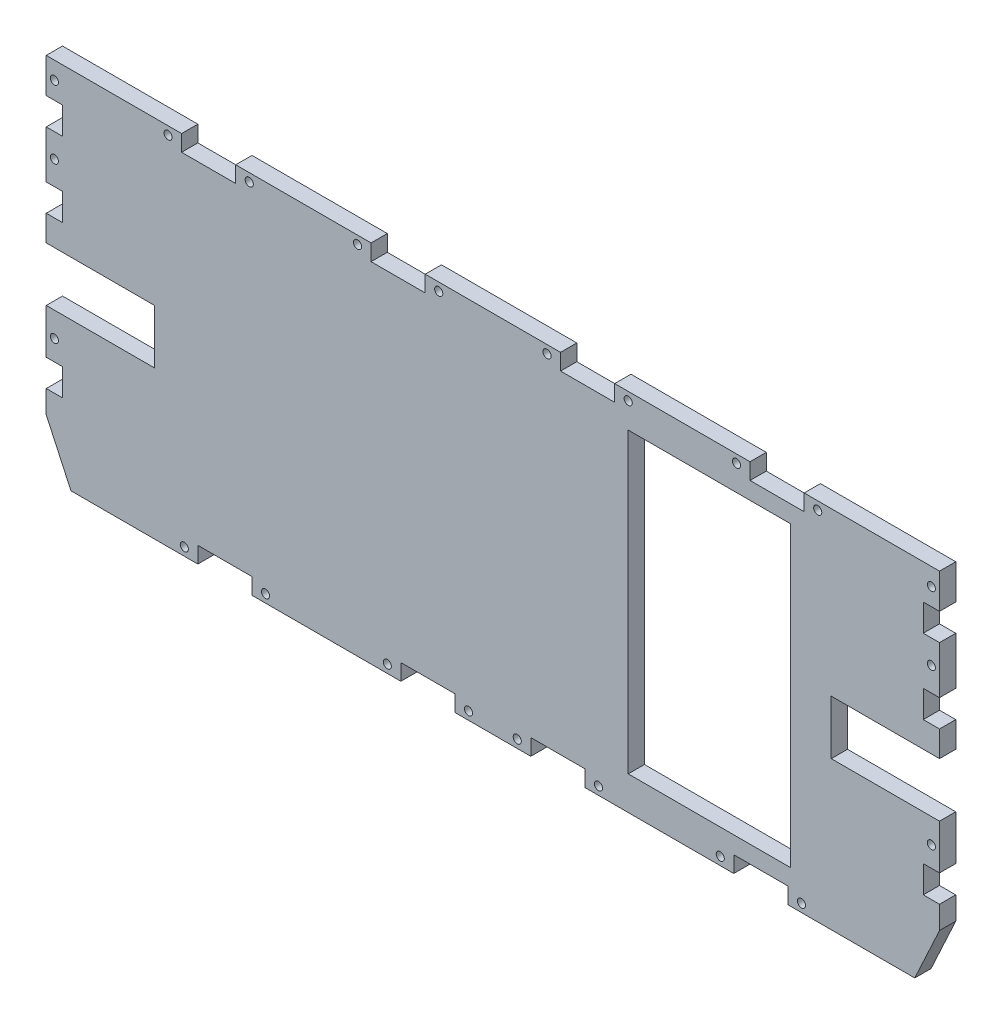
SolidWorks part; units mm, degrees
ref_plane "Plan de face" through (0, 0, 0) normal (0, 0, 1) x (1, 0, 0)
ref_plane "Plan de dessus" through (0, 0, 0) normal (0, 1, 0) x (1, 0, 0)
ref_plane "Plan de droite" through (0, 0, 0) normal (1, 0, 0) x (0, 0, -1)
sketch "Esquisse1" plane through (0, 0, 0) normal (0, 0, 1) x (1, 0, 0)
  line L0 (0, 124.9429) -> (0, -204.46) construction
  line L1 (-165, 96.73) -> (165, 96.73)
  line L2 (165, 96.73) -> (165, -18.27)
  line L3 (165, -18.27) -> (123, -109.0224)
  line L4 (123, -109.0224) -> (-123, -109.0224)
  line L5 (-211.9802, 0) -> (248.5953, 0) construction
  line L6 (-123, -109.0224) -> (-165, -18.27)
  line L7 (-165, -18.27) -> (-165, 96.73)
  dimension "D2" = 165
  dimension "D3" = 330
  dimension "D4" = 100
  dimension "D5" = 115
  dimension "D6" = 100
  dimension "D7" = 246
  dimension "D8" = 205.7524
  dimension "D9" = 96.73
  dimension "D10" = 115
extrude "Boss.-Extru.1" add sketch "Esquisse1" along normal blind 6
sketch "Esquisse3" plane through (0, 0, 0) normal (0, 0, -1) x (-1, 0, 0)
  line L0 (165, 96.73) -> (165, -18.27) construction
  line L1 (165, -9.85) -> (159, -9.85)
  line L2 (165, -9.85) -> (165, 0.15)
  line L3 (165, 0.15) -> (159, 0.15)
  line L4 (159, -9.85) -> (159, 0.15)
  line L5 (123, -109.0224) -> (-123, -109.0224) construction
  line L6 (165, 73.8526) -> (159, 73.8526)
  line L7 (165, 73.8526) -> (165, 83.8526)
  line L8 (165, 83.8526) -> (159, 83.8526)
  line L9 (159, 73.8526) -> (159, 83.8526)
  line L10 (-14, -38.02) -> (-14, -32.02)
  line L11 (109, -38.02) -> (89, -38.02)
  line L12 (109, -38.02) -> (109, -32.02)
  line L13 (109, -32.02) -> (89, -32.02)
  line L14 (-159, 46.23) -> (-159, 56.23)
  line L15 (0, -209.4812) -> (0, 177.1799) construction
  line L16 (-110, 84.355) -> (-50, 84.355)
  line L17 (-165, 56.23) -> (-159, 56.23)
  line L18 (89, -38.02) -> (89, -32.02)
  line L19 (34, -38.02) -> (14, -38.02)
  line L20 (34, -38.02) -> (34, -32.02)
  line L21 (34, -32.02) -> (14, -32.02)
  line L22 (-159, 73.8526) -> (-159, 83.8526)
  line L23 (-165, 83.8526) -> (-159, 83.8526)
  line L24 (-165, 73.8526) -> (-165, 83.8526)
  line L25 (-165, 73.8526) -> (-159, 73.8526)
  line L26 (-159, -9.85) -> (-159, 0.15)
  line L27 (-165, 0.15) -> (-159, 0.15)
  line L28 (-165, -9.85) -> (-165, 0.15)
  line L29 (-165, -9.85) -> (-159, -9.85)
  line L30 (-165, 96.73) -> (165, 96.73) construction
  line L31 (115, 96.73) -> (95, 96.73)
  line L32 (115, 96.73) -> (115, 90.73)
  line L33 (115, 90.73) -> (95, 90.73)
  line L34 (95, 96.73) -> (95, 90.73)
  line L35 (-25, 96.73) -> (-25, 90.73)
  line L36 (45, 96.73) -> (25, 96.73)
  line L37 (45, 96.73) -> (45, 90.73)
  line L38 (45, 90.73) -> (25, 90.73)
  line L39 (25, 96.73) -> (25, 90.73)
  line L40 (-45, 90.73) -> (-25, 90.73)
  line L41 (-45, 96.73) -> (-45, 90.73)
  line L42 (-45, 96.73) -> (-25, 96.73)
  line L43 (-95, 96.73) -> (-95, 90.73)
  line L44 (-115, 90.73) -> (-95, 90.73)
  line L45 (-115, 96.73) -> (-115, 90.73)
  line L46 (-115, 96.73) -> (-95, 96.73)
  line L47 (-165, 46.23) -> (-165, 56.23)
  line L48 (14, -38.02) -> (14, -32.02)
  line L49 (-34, -32.02) -> (-14, -32.02)
  line L50 (-34, -38.02) -> (-34, -32.02)
  line L51 (-34, -38.02) -> (-14, -38.02)
  line L52 (165, 46.23) -> (159, 46.23)
  line L53 (165, 46.23) -> (165, 56.23)
  line L54 (165, 56.23) -> (159, 56.23)
  line L55 (159, 46.23) -> (159, 56.23)
  line L56 (-165, 46.23) -> (-159, 46.23)
  line L57 (-89, -38.02) -> (-89, -32.02)
  line L58 (-109, -32.02) -> (-89, -32.02)
  line L59 (-109, -38.02) -> (-109, -32.02)
  line L60 (-109, -38.02) -> (-89, -38.02)
  line L61 (-165, -18.27) -> (-165, 96.73) construction
  line L62 (-110, 84.355) -> (-110, -25.645)
  line L63 (-110, -25.645) -> (-50, -25.645)
  line L64 (-50, 84.355) -> (-50, -25.645)
  line L66 (-165, 36.73) -> (-125, 36.73)
  line L67 (-165, 36.73) -> (-165, 16.73)
  line L68 (-165, 16.73) -> (-125, 16.73)
  line L69 (-125, 36.73) -> (-125, 16.73)
  line L70 (125, 36.73) -> (125, 16.73)
  line L71 (165, 16.73) -> (125, 16.73)
  line L72 (165, 36.73) -> (165, 16.73)
  line L73 (165, 36.73) -> (125, 36.73)
  dimension "D1" = 10
  dimension "D2" = 6
  dimension "D3" = 6
  dimension "D4" = 10
  dimension "D5" = 6
  dimension "D6" = 20
  dimension "D7" = 60
  dimension "D8" = 55
  dimension "D9" = 12.8774
  dimension "D10" = 20
  dimension "D11" = 20
  dimension "D12" = 50
  dimension "D13" = 50
  dimension "D14" = 6
  dimension "D15" = 110
  dimension "D16" = 56
  dimension "D17" = 15
  dimension "D18" = 6
  dimension "D19" = 10
  dimension "D20" = 40.5
  dimension "D21" = 6
  dimension "D22" = 6
  dimension "D23" = 20
  dimension "D24" = 71.0024
  dimension "D25" = 71.0024
  dimension "D26" = 60
  dimension "D27" = 20
  dimension "D28" = 40
  dimension "D29" = 6.375
  dimension "D30" = 8.42
extrude "Enlèv. mat.-Extru.2" cut sketch "Esquisse3" against normal blind 6
sketch "Esquisse4" plane through (0, 0, 0) normal (0, 0, -1) x (-1, 0, 0)
  line L0 (159, 73.8526) -> (165, 73.8526) construction
  line L1 (115, 90.73) -> (115, 96.73) construction
  line L2 (120.102, -35.02) -> (4.7601, -35.02) construction
  line L3 (14, -32.02) -> (14, -38.02) construction
  line L4 (34, -38.02) -> (34, -32.02) construction
  line L5 (89, -32.02) -> (89, -38.02) construction
  line L6 (115, 96.73) -> (165, 96.73) construction
  line L7 (109, -38.02) -> (109, -32.02) construction
  line L8 (165, 73.8526) -> (165, 56.23) construction
  line L9 (-120.102, -35.02) -> (-4.7601, -35.02) construction
  line L10 (165, 96.73) -> (165, 83.8526) construction
  line L11 (143.8632, 93.73) -> (-5, 93.73) construction
  line L12 (45, 96.73) -> (95, 96.73) construction
  line L14 (95, 96.73) -> (95, 90.73) construction
  line L15 (45, 90.73) -> (45, 96.73) construction
  line L16 (25, 96.73) -> (25, 90.73) construction
  line L17 (0, 142.2997) -> (0, -202.2086) construction
  line L18 (-162, -8.8123) -> (-162, 103.5881) construction
  line L19 (-80, 84.355) -> (-80, -25.645) construction
  line L21 (165, 0.15) -> (159, 0.15) construction
  line L22 (162, -8.8123) -> (162, 103.5881) construction
  line L25 (-50, 84.355) -> (-110, 84.355) construction
  line L26 (-110, -25.645) -> (-50, -25.645) construction
  circle A0 centre (162, 7.65) radius 1.5
  circle A1 centre (114, -35.02) radius 1.5
  circle A2 centre (162, 65.0426) radius 1.5
  circle A3 centre (84, -35.02) radius 1.5
  circle A4 centre (39, -35.02) radius 1.5
  circle A5 centre (162, 90.29) radius 1.5
  circle A6 centre (9, -35.02) radius 1.5
  circle A7 centre (-9, -35.02) radius 1.5
  circle A8 centre (-39, -35.02) radius 1.5
  circle A9 centre (-84, -35.02) radius 1.5
  circle A10 centre (120, 93.73) radius 1.5
  circle A11 centre (-114, -35.02) radius 1.5
  circle A12 centre (90, 93.73) radius 1.5
  circle A14 centre (50, 93.73) radius 1.5
  circle A15 centre (20, 93.73) radius 1.5
  circle A18 centre (-20, 93.73) radius 1.5
  circle A19 centre (-50, 93.73) radius 1.5
  circle A20 centre (-90, 93.73) radius 1.5
  circle A21 centre (-120, 93.73) radius 1.5
  circle A22 centre (-162, 90.29) radius 1.5
  circle A23 centre (-162, 65.0426) radius 1.5
  circle A24 centre (-162, 7.65) radius 1.5
  dimension "D1" = 3
  dimension "D3" = 3
  dimension "D10" = 3
  dimension "D11" = 3
  dimension "D12" = 3
  dimension "D13" = 5
  dimension "D14" = 5
  dimension "D18" = 3
  dimension "D19" = 3
  dimension "D29" = 3
  dimension "D31" = 3
  dimension "D33" = 3
  dimension "D34" = 3
  dimension "D40" = 5
  dimension "D5" = 7.5
  dimension "D8" = 5
  dimension "D15" = 5
  dimension "D16" = 5
  dimension "D9" = 3
  dimension "D6" = 8.81
  dimension "D7" = 6.44
  dimension "D24" = 3
  dimension "D26" = 3
  dimension "D28" = 3
  dimension "D38" = 5
  dimension "D42" = 5
extrude "Enlèv. mat.-Extru.3" cut sketch "Esquisse4" against normal blind 6
sketch "Esquisse5" plane through (0, 0, 0) normal (0, 0, -1) x (-1, 0, 0)
  line L0 (45, 96.73) -> (95, 96.73) construction
  line L1 (209.7155, -38.02) -> (-246.3297, -38.02)
  line L2 (209.7155, -38.02) -> (209.7155, -174.249)
  line L3 (209.7155, -174.249) -> (-246.3297, -174.249)
  line L4 (-246.3297, -38.02) -> (-246.3297, -174.249)
  dimension "D1" = 134.75
extrude "Enlèv. mat.-Extru.4" cut sketch "Esquisse5" against normal blind 6
